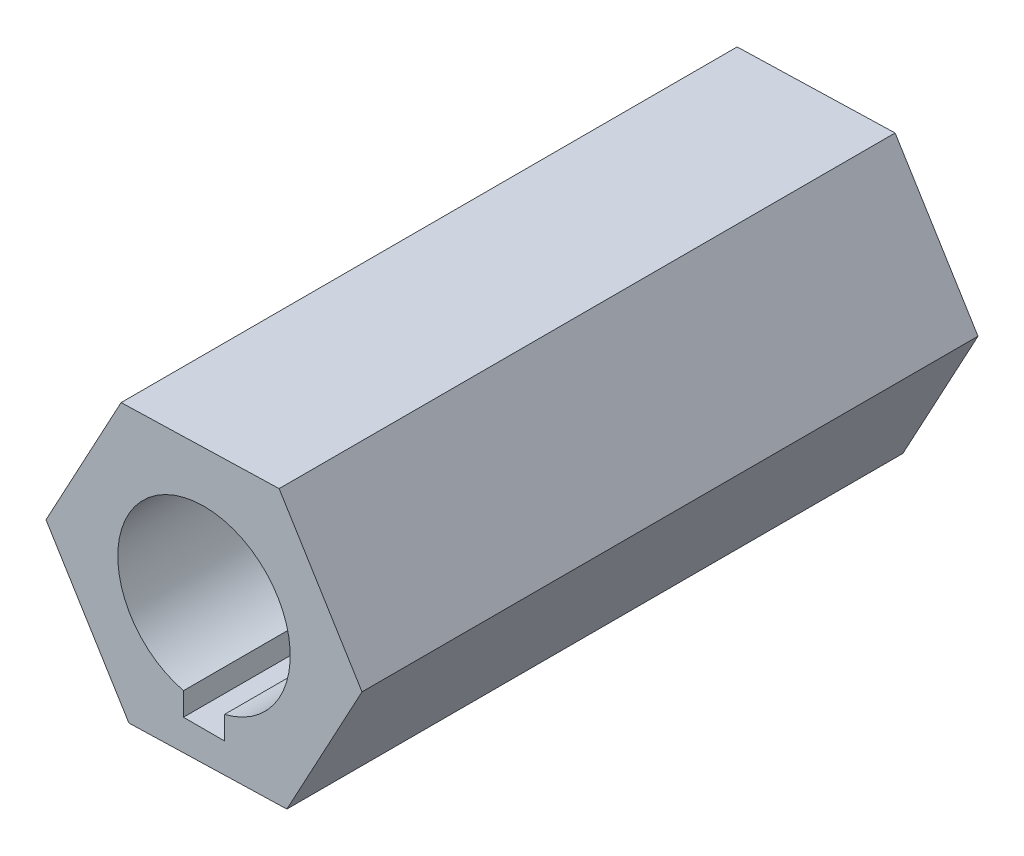
SolidWorks part; units mm, degrees
ref_plane "Front Plane" through (0, 0, 0) normal (0, 0, 1) x (1, 0, 0)
ref_plane "Top Plane" through (0, 0, 0) normal (0, 1, 0) x (1, 0, 0)
ref_plane "Right Plane" through (0, 0, 0) normal (1, 0, 0) x (0, 0, -1)
sketch "Sketch1" plane through (0, 0, 0) normal (0, 0, 1) x (1, 0, 0)
  line L1 (-7.3294, -0.2077) -> (-3.4848, -6.4513)
  line L2 (-3.4848, -6.4513) -> (3.8446, -6.2436)
  line L3 (3.8446, -6.2436) -> (7.3294, 0.2077)
  line L4 (7.3294, 0.2077) -> (3.4848, 6.4513)
  line L5 (3.4848, 6.4513) -> (-3.8446, 6.2436)
  line L6 (-3.8446, 6.2436) -> (-7.3294, -0.2077)
  circle A0 centre (0, 0) radius 6.35 construction
  circle A1 centre (0, 0) radius 4
  dimension "D1" = 8
  dimension "D2" = 12.7
extrude "Boss-Extrude1" add sketch "Sketch1" along normal blind 28.575
sketch "Sketch2" plane through (0, 0, 28.575) normal (0, 0, 1) x (1, 0, 0)
  line L1 (-0.9525, -3.0475) -> (0.9525, -3.0475)
  line L2 (-0.9525, -3.0475) -> (-0.9525, -4.9525)
  line L3 (-0.9525, -4.9525) -> (0.9525, -4.9525)
  line L4 (0.9525, -3.0475) -> (0.9525, -4.9525)
  line L5 (-0.9525, -3.0475) -> (0.9525, -4.9525) construction
  line L6 (-0.9525, -4.9525) -> (0.9525, -3.0475) construction
  circle A0 centre (0, 0) radius 4 construction
  point P0 (0, -4)
  dimension "D1" = 1.905
extrude "Cut-Extrude1" cut sketch "Sketch2" against normal through all
